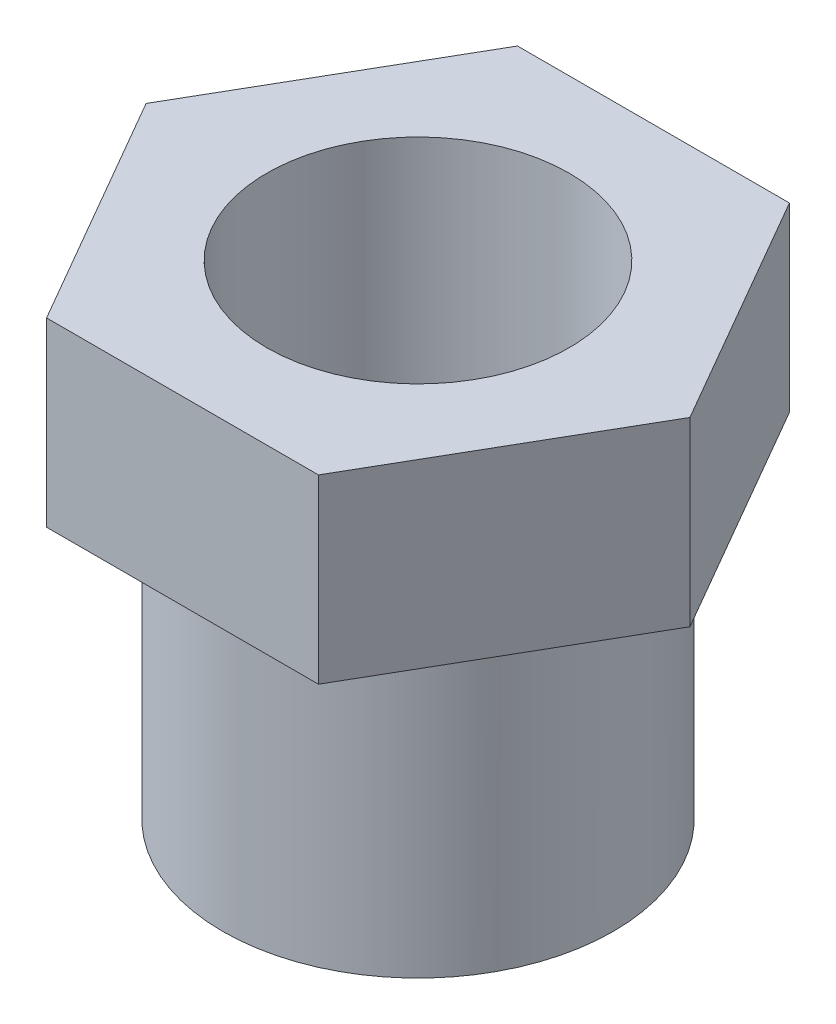
SolidWorks part; units mm, degrees
ref_plane "Alzado" through (0, 0, 0) normal (0, 0, 1) x (1, 0, 0)
ref_plane "Planta" through (0, 0, 0) normal (0, 1, 0) x (1, 0, 0)
ref_plane "Vista lateral" through (0, 0, 0) normal (1, 0, 0) x (0, 0, -1)
sketch "Croquis1" plane through (0, 0, 0) normal (0, 1, 0) x (1, 0, 0)
  line L1 (22.5, 0) -> (11.25, 19.4856)
  line L2 (11.25, 19.4856) -> (-11.25, 19.4856)
  line L3 (-11.25, 19.4856) -> (-22.5, 0)
  line L4 (-22.5, 0) -> (-11.25, -19.4856)
  line L5 (-11.25, -19.4856) -> (11.25, -19.4856)
  line L6 (11.25, -19.4856) -> (22.5, 0)
  circle A0 centre (0, 0) radius 19.4856 construction
  dimension "D1" = 45
extrude "Saliente-Extruir1" add sketch "Croquis1" along normal blind 15
sketch "Croquis2" plane through (0, 0, 0) normal (0, -1, 0) x (1, 0, 0)
  circle A0 centre (0, 0) radius 16.164
extrude "Saliente-Extruir2" add sketch "Croquis2" along normal blind 25
sketch "Croquis3" plane through (0, -25, 0) normal (0, -1, 0) x (1, 0, 0)
  circle A0 centre (0, 0) radius 17.1342
sketch "Croquis4" plane through (0, -45, 0) normal (0, -1, 0) x (1, 0, 0)
  circle A0 centre (0, 0) radius 12.5141
extrude "Cortar-Extruir1" cut sketch "Croquis4" against normal through all
